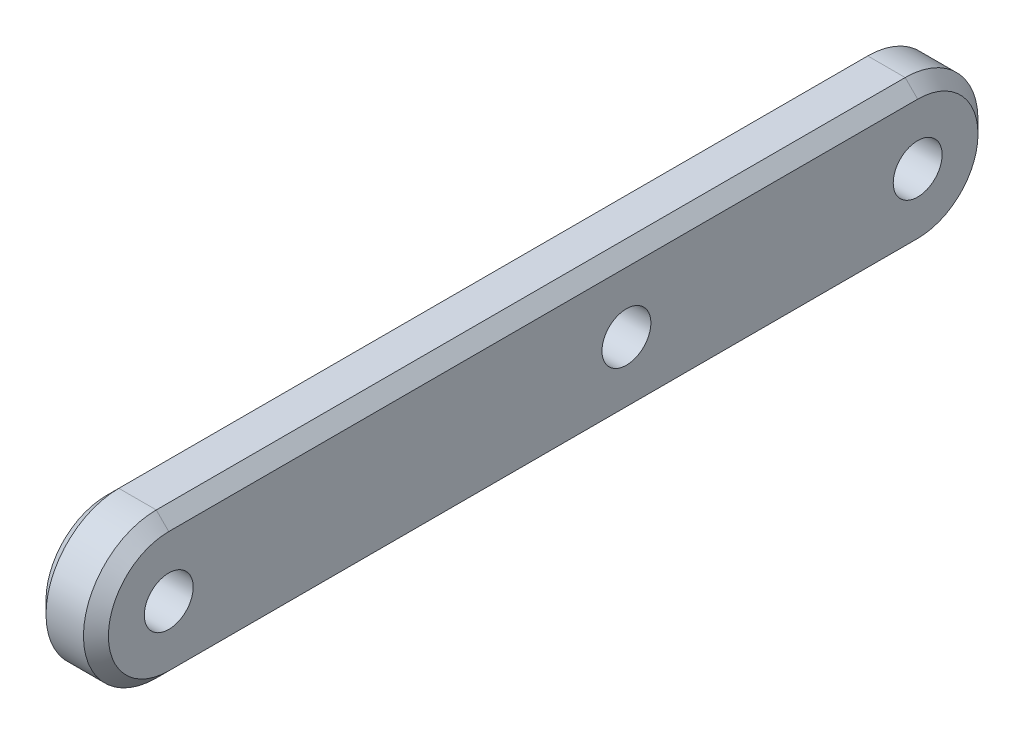
SolidWorks part; units mm, degrees
material "环氧树脂,未充填"
ref_plane "前视基准面" through (0, 0, 0) normal (0, 0, 1) x (1, 0, 0)
ref_plane "上视基准面" through (0, 0, 0) normal (0, 1, 0) x (1, 0, 0)
ref_plane "右视基准面" through (0, 0, 0) normal (1, 0, 0) x (0, 0, -1)
other "Configuration Table"
sketch "草图1" plane through (0, 0, 0) normal (1, 0, 0) x (0, 0, -1)
  line L0 (-18, 0) -> (18, 0) construction
  line L1 (18, 0) -> (4, 0) construction
  line L2 (-18, 0) -> (18, 0) construction
  line L3 (-18, 3.5) -> (18, 3.5)
  line L4 (-18, -3.5) -> (18, -3.5)
  circle A0 centre (18, 0) radius 0.85
  circle A1 centre (4, 0) radius 0.85
  circle A2 centre (-18, 0) radius 0.85
  arc A3 (-18, 3.5) -> (-18, -3.5) centre (-18, 0) ccw
  arc A4 (18, -3.5) -> (18, 3.5) centre (18, 0) ccw
  point P4 (0, 0)
  point P10 (0, 0)
  dimension "D3" = 1.7
  dimension "D4" = 3.5
  dimension "D5" = 1.7
  dimension "D6" = 1.7
  dimension "D1" = 22
  dimension "D2" = 14
extrude "凸台-拉伸1" add sketch "草图1" along normal mid plane 3
sketch "草图3" plane through (-1.5, 0, 0) normal (-1, 0, 0) x (0, 0, 1)
  circle A0 centre (-18, 0) radius 1.175
  circle A1 centre (-4, 0) radius 1.175
  circle A2 centre (18, 0) radius 1.175
  dimension "D1" = 2.35
extrude "切除-拉伸2" cut sketch "草图3" against normal through all both and the other way through all
chamfer "倒角1" distance 0.6 angle 45 8 edges at (1.5, 0, 21.5) (1.5, -3.5, 0) (1.5, 3.5, 0) (1.5, 0, -21.5) (-1.5, -3.5, 0) (-1.5, 0, -21.5) (-1.5, 0, 21.5) (-1.5, 3.5, 0)
